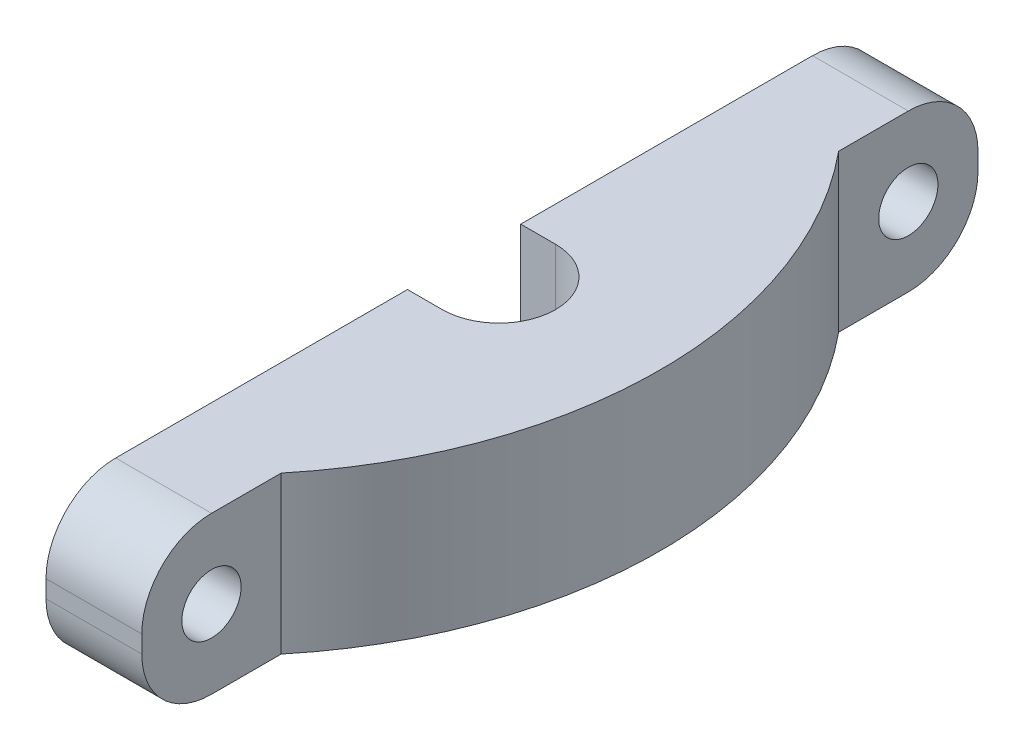
SolidWorks part; units mm, degrees
ref_plane "Front Plane" through (0, 0, 0) normal (0, 0, 1) x (1, 0, 0)
ref_plane "Top Plane" through (0, 0, 0) normal (0, 1, 0) x (1, 0, 0)
ref_plane "Right Plane" through (0, 0, 0) normal (1, 0, 0) x (0, 0, -1)
sketch "Sketch1" plane through (0, 0, 0) normal (1, 0, 0) x (0, 0, -1)
  line L0 (-24, 0) -> (24, 0) construction
  line L3 (-24, 0.5) -> (-24, -0.5)
  line L4 (24, 0.5) -> (24, -0.5)
  line L5 (-20, -4.5) -> (20, -4.5)
  line L6 (20, 4.5) -> (-20, 4.5)
  arc A2 (-24, 0.5) -> (-20, 4.5) centre (-20, 0.5) cw
  arc A3 (-24, -0.5) -> (-20, -4.5) centre (-20, -0.5) ccw
  arc A4 (24, -0.5) -> (20, -4.5) centre (20, -0.5) cw
  arc A5 (24, 0.5) -> (20, 4.5) centre (20, 0.5) ccw
  point P4 (0, 0)
  point P7 (-24, 0)
  point P12 (24, 0)
  point P18 (24, -4.5)
  point P21 (24, 4.5)
  dimension "D3" = 4
  dimension "D1" = 48
  dimension "D2" = 9
extrude "Boss-Extrude1" add sketch "Sketch1" along normal blind 11.25
sketch "Sketch2" plane through (0, -4.5, 0) normal (0, -1, 0) x (-1, 0, 0)
  line L0 (-2, -3.25) -> (0, -3.25)
  line L1 (0, -20) -> (0, 20) construction
  line L2 (-2, 3.25) -> (0, 3.25)
  line L3 (0, -3.25) -> (0, 3.25)
  arc A0 (-2, 3.25) -> (-2, -3.25) centre (-2, 0) ccw
  dimension "D1" = 6.5
  dimension "D2" = 2
extrude "Cut-Extrude1" cut sketch "Sketch2" against normal through all
sketch "Sketch3" plane through (11.25, 0, 0) normal (1, 0, 0) x (0, 0, -1)
  line L0 (-24, 0) -> (24, 0) construction
  line L1 (-24, 0.5) -> (-24, -0.5) construction
  line L2 (24, -0.5) -> (24, 0.5) construction
hole_wizard "M3 Clearance Hole1" positions "Sketch4" profile "Sketch6" hole size "M3" standard "ISO" end condition through all
sketch "Sketch4" plane through (11.25, 0, 0) normal (1, 0, 0) x (0, 0, -1)
  line L0 (-24, 0) -> (24, 0) construction
  line L1 (24, -0.5) -> (24, 0.5) construction
  line L2 (-24, 0.5) -> (-24, -0.5) construction
  point P0 (-20, 0)
  point P4 (20, 0)
  dimension "D1" = 4
  dimension "D2" = 4
sketch "Sketch6" plane through (11.25, 0, 20) normal (0, 1, 0) x (0, 0, -1)
  line L0 (0, 0) -> (0, 11.25)
  line L1 (0, 11.25) -> (1.7, 11.25)
  line L2 (1.7, 11.25) -> (1.7, 0)
  line L5 (1.7, 0) -> (0, 0)
  line L11 (0, -6.35) -> (0, 107.95) construction
  dimension "Thru Hole Dia." = 3.4
  dimension "Thru Hole Depth" = 11.25
sketch "Sketch7" plane through (0, -4.5, 0) normal (0, -1, 0) x (-1, 0, 0)
  line L0 (-5.5, -24) -> (-5.5, -16)
  line L1 (-11.25, -24) -> (0, -24) construction
  line L2 (-5.5, 24) -> (-5.5, 16)
  line L3 (-11.25, 24) -> (0, 24) construction
  line L4 (0, -20) -> (0, -3.25) construction
  line L6 (-11.25, -24) -> (-11.25, 24) construction
  line L7 (-5.5, -24) -> (-11.25, -24)
  line L8 (-11.25, -24) -> (-11.25, 24)
  line L9 (-11.25, 24) -> (-5.5, 24)
  arc A0 (-5.5, -16) -> (-5.5, 16) centre (13.8859, 0) cw
  point P11 (-11.25, 0)
  point P14 (-11.25, 0)
  line M6 (0, 20) -> (-11.25, 20)
  line M7 (-11.25, 20) -> (-11.25, -20)
  line M8 (-11.25, -20) -> (0, -20)
  dimension "D1" = 5.5
  dimension "D2" = 8
extrude "Cut-Extrude2" cut sketch "Sketch7" against normal through all contours L8 L7 L0 M8 | L0 A0 L8 M8 | A0 L2 M7 M6 | L9 L8 L2 M6
